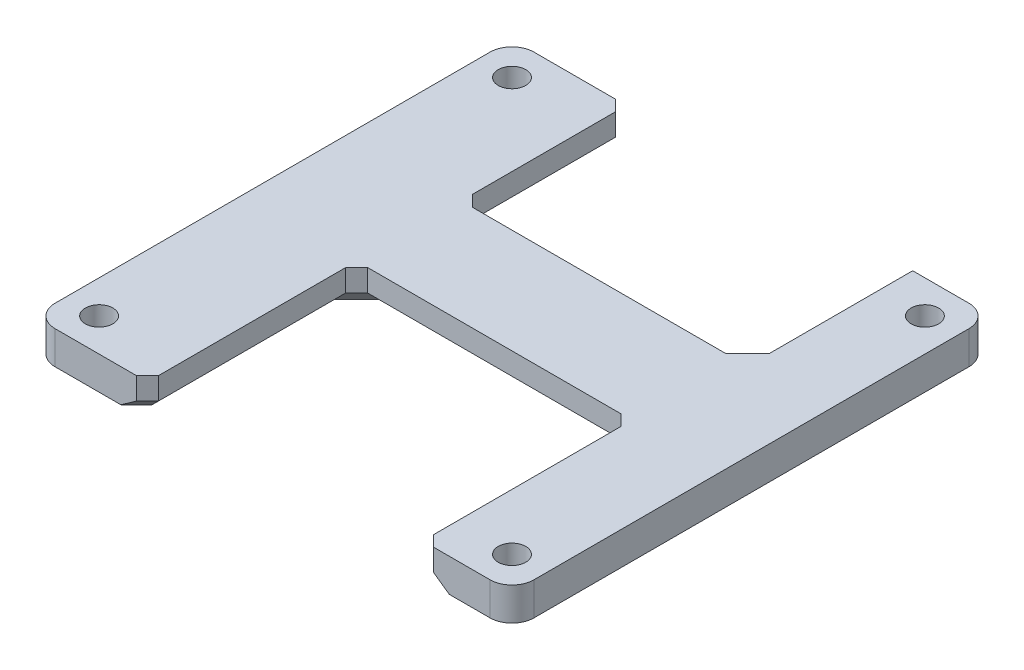
SolidWorks part; units mm, degrees
ref_plane "Alzado" through (0, 0, 0) normal (0, 0, 1) x (1, 0, 0)
ref_plane "Planta" through (0, 0, 0) normal (0, 1, 0) x (1, 0, 0)
ref_plane "Vista lateral" through (0, 0, 0) normal (1, 0, 0) x (0, 0, -1)
sketch "Croquis1" plane through (0, 0, 0) normal (0, 1, 0) x (1, 0, 0)
  point P0 (0, 0)
  line B0 (-31.1088, -40.5) -> (-30.1088, -39.5)
  line B1 (-30.1088, -39.5) -> (-30.1088, -21.5)
  line B2 (-30.1088, -21.5) -> (-5.1088, -21.5)
  line B3 (-38.5, -40.5) -> (-31.1088, -40.5)
  line B4 (-40.5, -38.5) -> (-40.5, 1)
  line B5 (-38.5, 3) -> (-31.1088, 3)
  line B6 (3, -38.5) -> (3, 1)
  line B7 (-5.1088, -21.5) -> (-5.1088, -39.5)
  line B8 (-5.1088, -39.5) -> (-4.1088, -40.5)
  line B9 (-4.1088, -40.5) -> (1, -40.5)
  line B10 (-31.1088, 3) -> (-30.1088, 2)
  line B11 (-30.1088, 2) -> (-30.1088, -11)
  line B12 (-30.1088, -11) -> (-29.1088, -12)
  line B13 (-29.1088, -12) -> (-6.1088, -12)
  line B14 (-6.1088, -12) -> (-5.1088, -11)
  line B15 (-5.1088, -11) -> (-5.1088, 2)
  line B16 (-5.1088, 2) -> (-4.1088, 3)
  line B17 (-4.1088, 3) -> (1, 3)
  circle B18 centre (-37.5, -37.5) radius 1.25
  circle B19 centre (-37.5, 0) radius 1.25
  circle B20 centre (0, -37.5) radius 1.25
  circle B21 centre (0, 0) radius 1.25
  arc B22 (1, 3) -> (3, 1) centre (1, 1) cw
  arc B23 (-40.5, 1) -> (-38.5, 3) centre (-38.5, 1) cw
  arc B24 (-38.5, -40.5) -> (-40.5, -38.5) centre (-38.5, -38.5) cw
  arc B25 (1, -40.5) -> (3, -38.5) centre (1, -38.5) ccw
sketch_block_instance "Bloque1-2"
sketch_block "Bloque1" parameters "D1"=2
extrude "Saliente-Extruir1" add sketch "Croquis1" along normal blind 3
chamfer "Chaflán1" distance 1 angle 45 14 edges at (-4.6088, 0, 40) (-30.6088, 0, 40) (-4.6088, 0, -2.5) (-5.1088, 3, 4.5) (-30.6088, 0, -2.5) (-5.6088, 0, 11.5) (-30.1088, 0, 4.5) (-29.6088, 0, 11.5) (-17.6088, 0, 12) (-5.1088, 0, 30.5) (-30.1088, 0, 30.5) (-5.1088, 1.5, 21.5) (-17.6088, 0, 21.5) (-30.1088, 1.5, 21.5)
